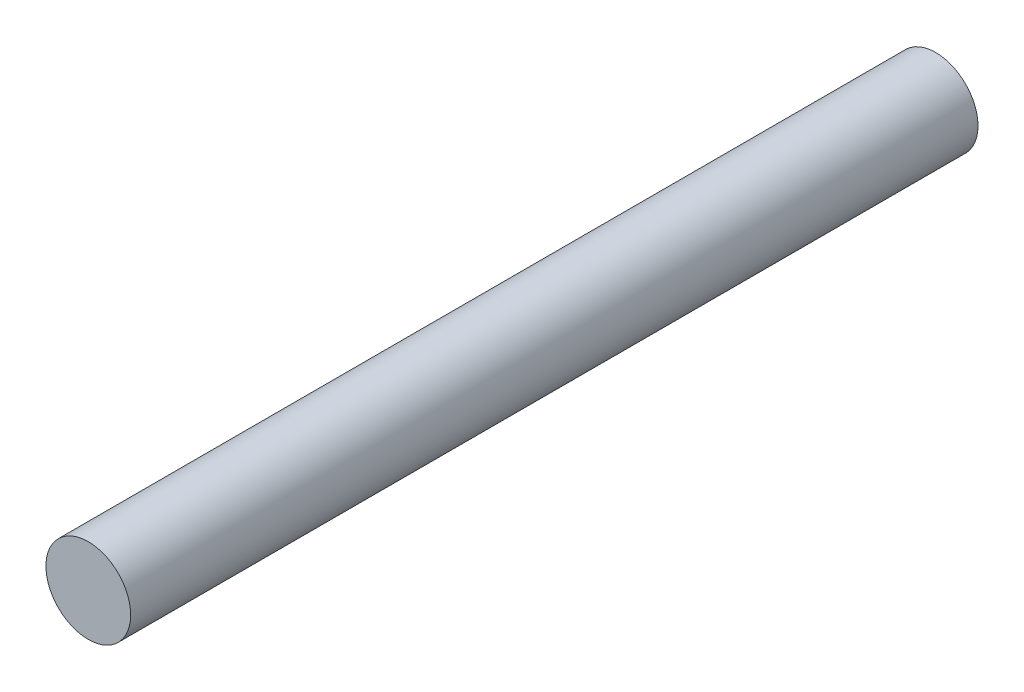
SolidWorks part; units mm, degrees
ref_plane "Plan de face" through (0, 0, 0) normal (0, 0, 1) x (1, 0, 0)
ref_plane "Plan de dessus" through (0, 0, 0) normal (0, 1, 0) x (1, 0, 0)
ref_plane "Plan de droite" through (0, 0, 0) normal (1, 0, 0) x (0, 0, -1)
sketch "Esquisse1" plane through (0, 0, 0) normal (0, 0, 1) x (1, 0, 0)
  circle A0 centre (0, 0) radius 1.5
  dimension "D1" = 3
extrude "Boss.-Extru.1" add sketch "Esquisse1" along normal blind 30
